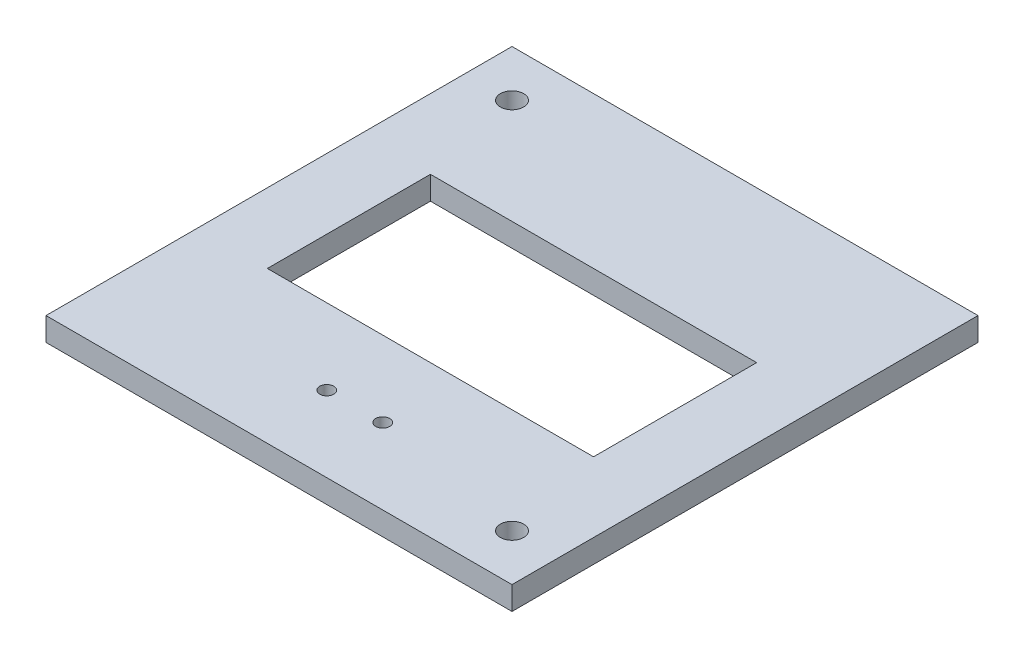
SolidWorks part; units mm, degrees
ref_plane "Front Plane" through (0, 0, 0) normal (0, 0, 1) x (1, 0, 0)
ref_plane "Top Plane" through (0, 0, 0) normal (0, 1, 0) x (1, 0, 0)
ref_plane "Right Plane" through (0, 0, 0) normal (1, 0, 0) x (0, 0, -1)
sketch "Sketch1" plane through (0, 0, 0) normal (0, 1, 0) x (1, 0, 0)
  line L0 (-50, 32.5) -> (-50, 0) construction
  line L1 (-100, 100) -> (0, 100)
  line L2 (-100, 100) -> (-100, 0)
  line L3 (-100, 0) -> (0, 0)
  line L4 (0, 100) -> (0, 0)
  line L5 (-85, 67.5) -> (-15, 67.5)
  line L6 (-85, 67.5) -> (-85, 32.5)
  line L7 (-85, 32.5) -> (-15, 32.5)
  line L8 (-15, 67.5) -> (-15, 32.5)
  line L9 (-56, 16.25) -> (-44, 16.25) construction
  line L10 (-90, 90) -> (-90, 100) construction
  line L11 (-90, 90) -> (-100, 90) construction
  line L12 (-10, 10) -> (0, 10) construction
  line L13 (-10, 10) -> (-10, 0) construction
  circle A1 centre (-56, 16.25) radius 1.5
  circle A2 centre (-44, 16.25) radius 1.5
  circle A3 centre (-90, 90) radius 2.5
  circle A4 centre (-10, 10) radius 2.5
  point P8 (-85, 50)
  point P9 (-100, 50)
  point P10 (-50, 100)
  point P11 (-50, 67.5)
  point P18 (-50, 16.25)
  point P19 (-50, 16.25)
  dimension "D5" = 12
  dimension "D6" = 3
  dimension "D7" = 3
  dimension "D8" = 5
  dimension "D9" = 5
  dimension "D1" = 100
  dimension "D2" = 100
  dimension "D3" = 35
  dimension "D4" = 70
  dimension "D10" = 10
  dimension "D11" = 10
extrude "Boss-Extrude1" add sketch "Sketch1" along normal blind 5
